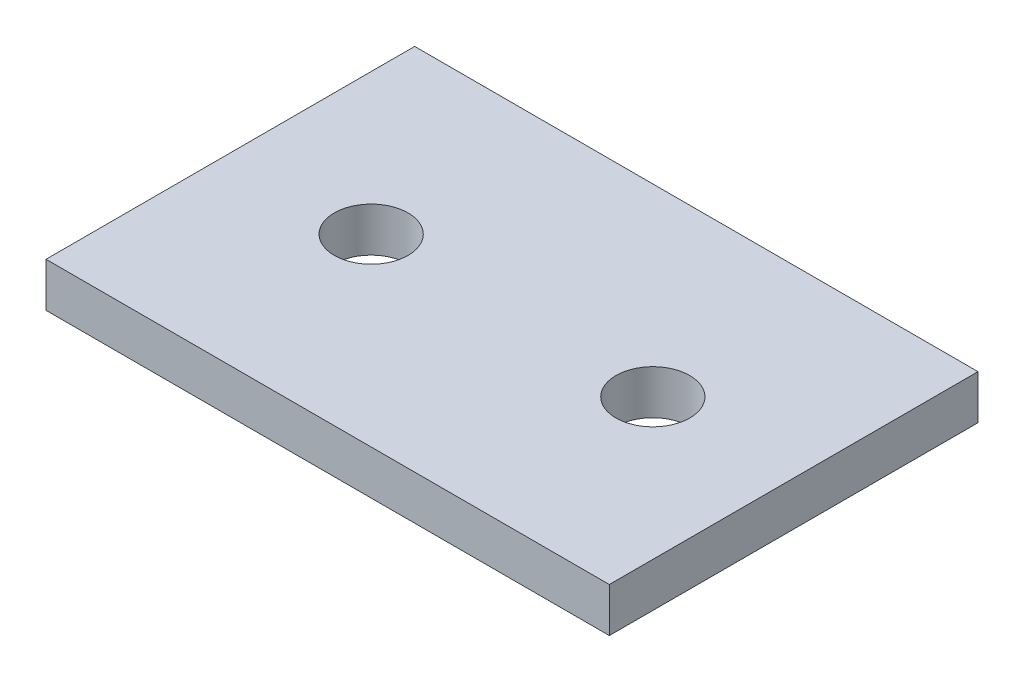
SolidWorks part; units mm, degrees
ref_plane "Alzado" through (0, 0, 0) normal (0, 0, 1) x (1, 0, 0)
ref_plane "Planta" through (0, 0, 0) normal (0, 1, 0) x (1, 0, 0)
ref_plane "Vista lateral" through (0, 0, 0) normal (1, 0, 0) x (0, 0, -1)
sketch "Croquis1" plane through (0, 0, 0) normal (0, 1, 0) x (1, 0, 0)
  line L1 (0, 0) -> (-38.2, 0)
  line L2 (0, 0) -> (0, 25)
  line L3 (0, 25) -> (-38.2, 25)
  line L4 (-38.2, 0) -> (-38.2, 25)
  dimension "D1" = 25
  dimension "D2" = 38.2
extrude "Saliente-Extruir1" add sketch "Croquis1" along normal blind 3
sketch "Croquis2" plane through (0, 3, 0) normal (0, 1, 0) x (1, 0, 0)
  line L0 (-19.1, 25) -> (-19.1, 0) construction
  line L1 (0, 25) -> (-38.2, 25) construction
  line L2 (-38.2, 0) -> (0, 0) construction
  line L3 (0, 12.5) -> (-38.2, 12.5) construction
  line L4 (-38.2, 25) -> (-38.2, 0) construction
  circle A0 centre (-28.65, 12.5) radius 2.5
  circle A1 centre (-9.55, 12.5) radius 2.5
  point P11 (-19.1, 12.5)
  dimension "D2" = 5
  dimension "D1" = 9.55
extrude "Cortar-Extruir1" cut sketch "Croquis2" against normal blind 3 contours A0 | A1
